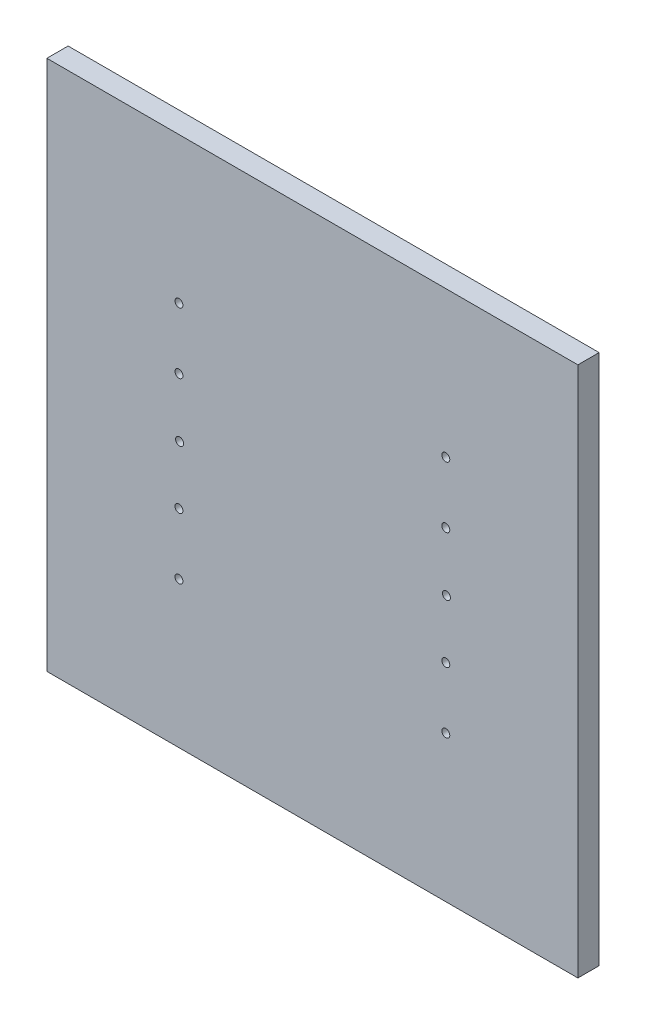
SolidWorks part; units mm, degrees
ref_plane "正面" through (0, 0, 0) normal (0, 0, 1) x (1, 0, 0)
ref_plane "平面" through (0, 0, 0) normal (0, 1, 0) x (1, 0, 0)
ref_plane "右側面" through (0, 0, 0) normal (1, 0, 0) x (0, 0, -1)
sketch "Sketch1" plane through (0, 0, 0) normal (0, 0, 1) x (1, 0, 0)
  line L1 (0, 0) -> (200, 0)
  line L2 (0, 0) -> (0, 200)
  line L3 (0, 200) -> (200, 200)
  line L4 (200, 0) -> (200, 200)
extrude "Boss-Extrude1" add sketch "Sketch1" along normal blind 8
sketch "Sketch2" plane through (0, 0, 8) normal (0, 0, 1) x (1, 0, 0)
  line L0 (0, 200) -> (0, 0) construction
  line L1 (50, 150) -> (150, 150)
  line L2 (50, 150) -> (50, 50)
  line L3 (50, 50) -> (150, 50)
  line L4 (150, 150) -> (150, 50)
  line L5 (200, 0) -> (200, 200) construction
  line L6 (200, 200) -> (0, 200) construction
  line L8 (48, 152) -> (152, 152)
  line L9 (48, 152) -> (48, 48)
  line L10 (48, 48) -> (152, 48)
  line L11 (152, 152) -> (152, 48)
  dimension "D1" = 100
  dimension "D2" = 50
  dimension "D3" = 50
  dimension "D4" = 100
  dimension "D5" = 50
  dimension "D6" = 2
  dimension "D7" = 2
  dimension "D8" = 2
  dimension "D9" = 2
sketch "Sketch5" plane through (0, 0, 0) normal (0, 0, -1) x (-1, 0, 0)
  line L0 (-150, 150) -> (-150, 50) construction
  line L1 (-49.75, 150.25) -> (-150.25, 150.25)
  line L2 (-49.75, 150.25) -> (-49.75, 49.75)
  line L3 (-49.75, 49.75) -> (-150.25, 49.75)
  line L4 (-150.25, 150.25) -> (-150.25, 49.75)
  line L5 (-50, 50) -> (-150, 50) construction
  dimension "D1" = 100.5
  dimension "D2" = 100.5
  dimension "D3" = 0.25
  dimension "D4" = 0.25
hole_wizard "CBORE for M2 Pan Head Screw1" positions "3DSketch1" profile "Sketch6" counterbore size "M2" standard "JIS"
sketch3d "3DSketch1"
  line L0 (49.75, 150.25, 0) -> (49.75, 49.75, 0) construction
  line L1 (200, 200, 0) -> (0, 200, 0) construction
  circle A0 centre (150.25, 145, 8) radius 0.8 construction
  point P23 (49.75, 55, 15.4807)
  point P26 (49.75, 78, 15.4807)
  point P29 (49.75, 100, 15.4807)
  point P32 (49.75, 122, 15.4807)
  point P35 (49.75, 145, 15.4807)
  point P38 (150.25, 55, 15.4807)
  point P41 (150.25, 55, 15.4807)
  point P43 (150.25, 78, 15.4807)
  point P46 (150.25, 100, 15.4807)
  point P49 (150.25, 122, 15.4807)
  point P52 (150.25, 145, 8)
  point P56 (150.25, 145, 7.2)
  point P73 (49.75, 145, 0)
  point P80 (49.75, 121.9969, 0)
  point P82 (49.75, 100, 0)
  point P84 (49.75, 78.0125, 0)
  point P86 (49.75, 55.0095, 0)
  point P91 (49.75, 100, 0)
  dimension "D1" = 55
  dimension "D2" = 23
  dimension "D3" = 23
sketch "Sketch6" plane through (49.75, 55.0095, 0) normal (1, 0, 0) x (0, 1, 0)
  line L0 (0, 0) -> (0, 8.9013)
  line L1 (0, 8.9013) -> (1.5, 8)
  line L2 (1.5, 8) -> (1.5, 4)
  line L3 (1.5, 4) -> (2.5, 4)
  line L4 (2.5, 4) -> (2.5, 0)
  line L5 (2.5, 0) -> (0, 0)
  line L10 (0, 8.9013) -> (-1.5, 8) construction
  line L11 (0, -6.35) -> (0, 107.95) construction
  dimension "Hole Dia." = 3
  dimension "Hole Depth" = 8
  dimension "C'Bore Dia." = 5
  dimension "C'Bore Depth" = 4
  dimension "Drill Angle" = 118
sketch "Sketch7" plane through (0, 0, 0) normal (0, 0, -1) x (-1, 0, 0)
  line L0 (-50, 150) -> (-50, 50) construction
  circle A0 centre (-50, 100) radius 2.5
extrude "Cut-Extrude1" cut sketch "Sketch7" against normal blind 4
sketch "Sketch9" plane through (0, 0, 4) normal (0, 0, -1) x (-1, 0, 0)
  line L0 (-50, 150) -> (-50, 50) construction
  circle A0 centre (-50, 100) radius 1.5
extrude "Cut-Extrude2" cut sketch "Sketch9" against normal blind 10
pattern_linear "LPattern1" count 2 spacing 100.5 along (1, 0, 0) of "CBORE for M2 Pan Head Screw1", "Cut-Extrude1", "Cut-Extrude2"
